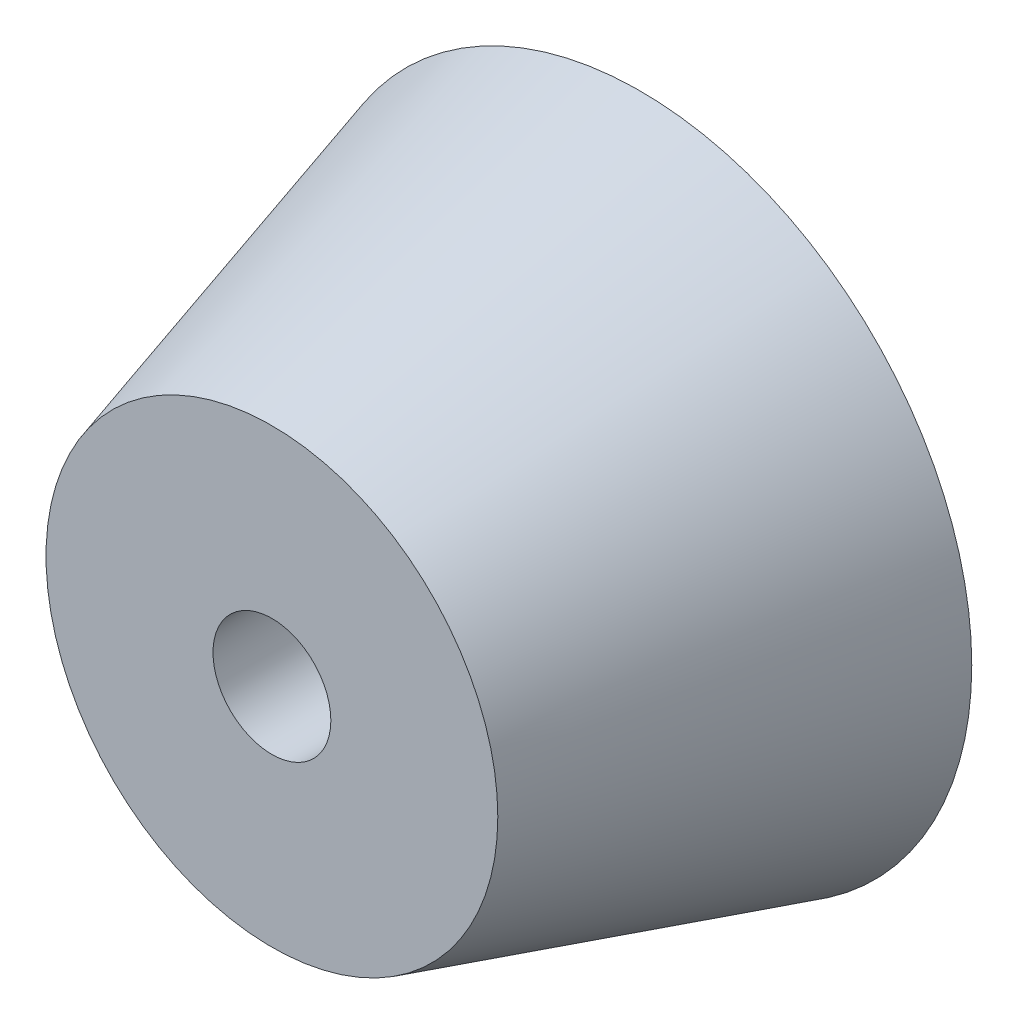
SolidWorks part; units mm, degrees
material "ABS"
ref_plane "Plano frontal" through (0, 0, 0) normal (0, 0, 1) x (1, 0, 0)
ref_plane "Plano superior" through (0, 0, 0) normal (0, 1, 0) x (1, 0, 0)
ref_plane "Plano direito" through (0, 0, 0) normal (1, 0, 0) x (0, 0, -1)
sketch "Esboço1" plane through (0, 0, -36.1) normal (0, 0, 1) x (1, 0, 0)
  circle A0 centre (-45.5704, -345.9355) radius 9
  dimension "D1" = 18
extrude "Ressalto-extrusão1" add sketch "Esboço1" along normal blind 10 draft 16
hole_wizard "M3 Clearance Hole1" positions "Sketch2" profile "Sketch1" hole size "M3" standard "ISO" end condition through all
sketch "Sketch2" plane through (0, 0, -26.1) normal (0, 0, 1) x (1, 0, 0)
  point P0 (-45.5704, -345.9355)
sketch "Sketch1" plane through (-45.5704, -345.9355, -26.1) normal (1, 0, 0) x (0, -1, 0)
  line L0 (0, 0) -> (0, 10)
  line L1 (0, 10) -> (1.6, 10)
  line L2 (1.6, 10) -> (1.6, 0)
  line L5 (1.6, 0) -> (0, 0)
  line L11 (0, -6.35) -> (0, 107.95) construction
  dimension "Thru Hole Dia." = 3.2
  dimension "Thru Hole Depth" = 10
